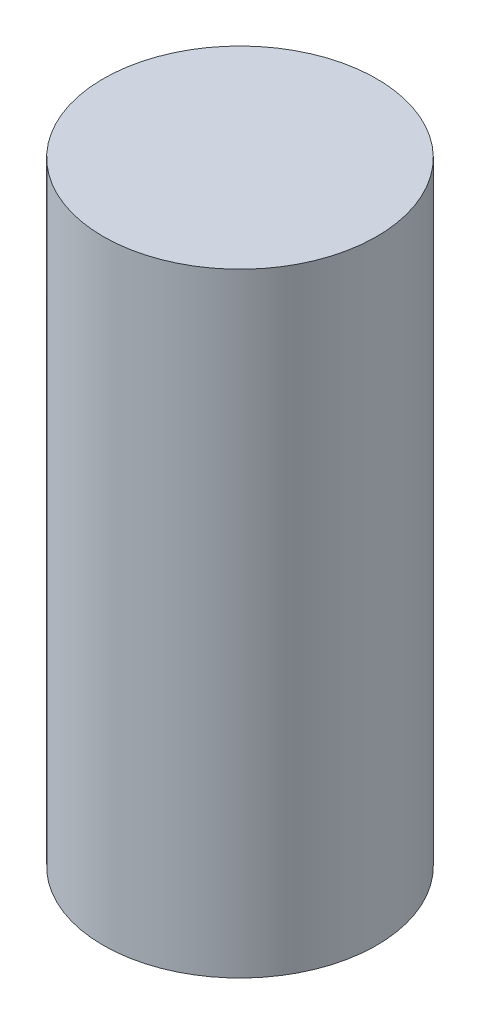
SolidWorks part; units mm, degrees
ref_plane "Front Plane" through (0, 0, 0) normal (0, 0, 1) x (1, 0, 0)
ref_plane "Top Plane" through (0, 0, 0) normal (0, 1, 0) x (1, 0, 0)
ref_plane "Right Plane" through (0, 0, 0) normal (1, 0, 0) x (0, 0, -1)
sketch "Sketch1" plane through (0, 0, 0) normal (0, 1, 0) x (1, 0, 0)
  circle A0 centre (0, 0) radius 6.223
  dimension "D1" = 12.446
extrude "Boss-Extrude1" add sketch "Sketch1" along normal blind 27.94
